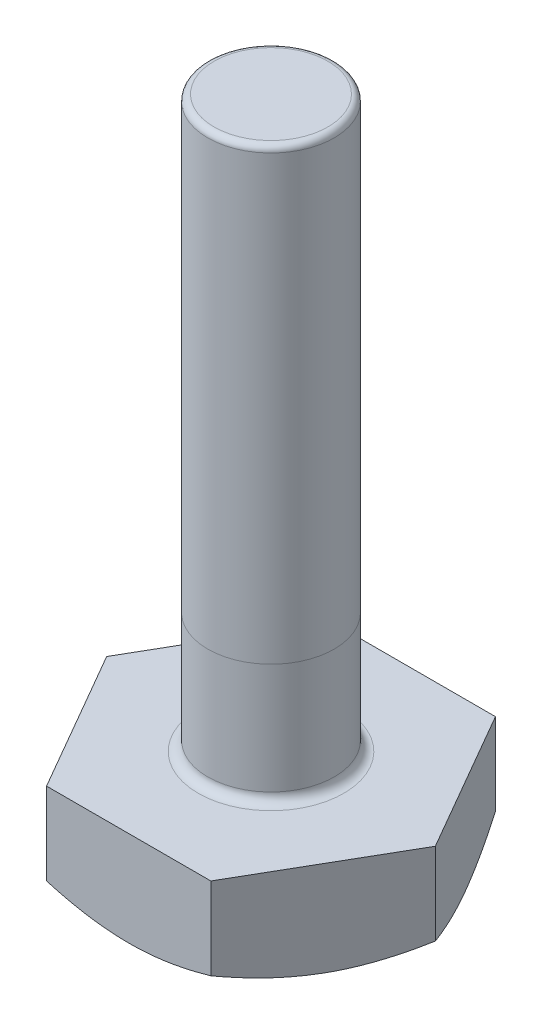
SolidWorks part; units mm, degrees
ref_plane "Front Plane" through (0, 0, 0) normal (0, 0, 1) x (1, 0, 0)
ref_plane "Top Plane" through (0, 0, 0) normal (0, 1, 0) x (1, 0, 0)
ref_plane "Right Plane" through (0, 0, 0) normal (1, 0, 0) x (0, 0, -1)
sketch "Sketch1" plane through (0, 0, 0) normal (0, 1, 0) x (1, 0, 0)
  line L1 (2.5981, 0) -> (1.299, 2.25)
  line L2 (1.299, 2.25) -> (-1.299, 2.25)
  line L3 (-1.299, 2.25) -> (-2.5981, 0)
  line L4 (-2.5981, 0) -> (-1.299, -2.25)
  line L5 (-1.299, -2.25) -> (1.299, -2.25)
  line L6 (1.299, -2.25) -> (2.5981, 0)
  circle A0 centre (0, 0) radius 2.25 construction
  circle A1 centre (0, 0) radius 1 construction
  dimension "D1" = 2
  dimension "D2" = 4.5
extrude "Boss-Extrude2" add sketch "Sketch1" along normal blind 1.5
sketch "Sketch2" plane through (0, 0, 0) normal (0, 1, 0) x (1, 0, 0)
  line L6 (2.5981, 0) -> (1.299, 2.25)
  line L7 (1.299, 2.25) -> (-1.299, 2.25)
  line L8 (-1.299, 2.25) -> (-2.5981, 0)
  line L9 (-2.5981, 0) -> (-1.299, -2.25)
  line L10 (-1.299, -2.25) -> (1.299, -2.25)
  line L11 (1.299, -2.25) -> (2.5981, 0)
  line L12 (2.5981, 0) -> (1.299, 2.25)
  line L13 (1.299, 2.25) -> (-1.299, 2.25)
  line L14 (-1.299, 2.25) -> (-2.5981, 0)
  line L15 (-2.5981, 0) -> (-1.299, -2.25)
  line L16 (-1.299, -2.25) -> (1.299, -2.25)
  line L17 (1.299, -2.25) -> (2.5981, 0)
  circle A0 centre (0, 0) radius 2.25 construction
  circle A1 centre (0, 0) radius 2.25
  dimension "D1" = 0
extrude "Cut-Extrude1" cut sketch "Sketch2" along normal blind 1.5 draft 60 flip side to cut contours A1
sketch "Sketch3" plane through (0, 1.5, 0) normal (0, 1, 0) x (1, 0, 0)
  circle A0 centre (0, 0) radius 1 construction
  circle A1 centre (0, 0) radius 1
extrude "Boss-Extrude3" add sketch "Sketch3" along normal blind 9
fillet "Fillet1" radius 0.1 1 edges at (0, 10.5, 1)
fillet "Fillet2" radius 0.15 1 edges at (0, 1.5, 1)
sketch "Sketch4" plane through (0, 0, 0) normal (0, 0, 1) x (1, 0, 0)
  line L0 (-3.9898, 3.4) -> (3.9898, 3.4)
  line L1 (-1, 10.4) -> (1, 10.4) construction
  point P2 (0, 3.4)
  dimension "D1" = 7
split line "Split Line2"
